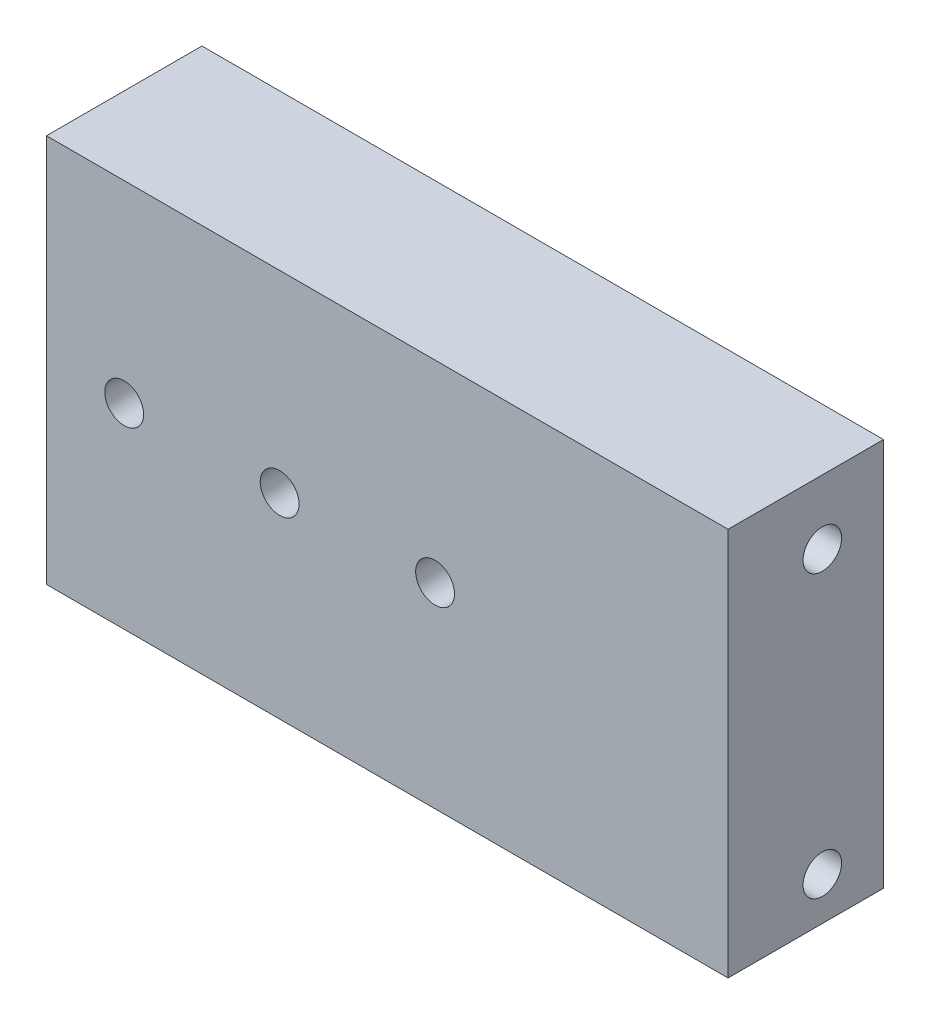
SolidWorks part; units mm, degrees
material "Delrin 2700 NC010, Low Viscosity Acetal Copolymer (SS)"
ref_plane "Front Plane" through (0, 0, 0) normal (0, 0, 1) x (1, 0, 0)
ref_plane "Top Plane" through (0, 0, 0) normal (0, 1, 0) x (1, 0, 0)
ref_plane "Right Plane" through (0, 0, 0) normal (1, 0, 0) x (0, 0, -1)
sketch "Sketch1" plane through (0, 0, 0) normal (1, 0, 0) x (0, 0, -1)
  line L0 (25.4, 0) -> (25.4, 108.2)
  line L1 (0, 0) -> (25.4, 0)
  line L2 (0, 0) -> (0, 63.5)
  line L3 (0, 63.5) -> (25.4, 63.5)
  line L4 (25.4, 0) -> (25.4, 63.5)
  line L5 (25.4, 108.2) -> (0, 108.2)
  line L6 (0, 108.2) -> (0, 0)
  line L7 (25.4, 108.2) -> (228.6, 108.2) construction
  dimension "D1" = 25.4
  dimension "D2" = 63.5
  dimension "D3" = 44.7
extrude "Boss-Extrude1" add sketch "Sketch1" against normal up to surface (111.376 mm away) contours L2 L1 L0 L3
hole_wizard "1/4 (0.25) Diameter Hole1" positions "Sketch2" profile "Sketch3" hole size "1/4" standard "ANSI Inch" end condition through all
sketch "Sketch2" plane through (0, 0, 0) normal (0, 0, 1) x (1, 0, 0)
  point P0 (-98.676, 32)
  point P3 (-47.876, 32)
  point P6 (-73.276, 32)
sketch "Sketch3" plane through (-98.676, 32, 0) normal (1, 0, 0) x (0, -1, 0)
  line L0 (0, 0) -> (0, 25.4)
  line L1 (0, 25.4) -> (3.175, 25.4)
  line L2 (3.175, 25.4) -> (3.175, 0)
  line L5 (3.175, 0) -> (0, 0)
  line L11 (0, -6.35) -> (0, 107.95) construction
  dimension "Thru Hole Dia." = 6.35
  dimension "Thru Hole Depth" = 25.4
hole_wizard "Ø6.0mm Dowel Hole1" positions "Sketch4" profile "Sketch6" hole size "Ø6.0" standard "ANSI Metric"
sketch "Sketch4" plane through (0, 0, 0) normal (1, 0, 0) x (0, 0, -1)
  point P0 (15.4, 7)
  point P3 (15.4, 53)
sketch "Sketch6" plane through (0, 7, -15.4) normal (0, 1, 0) x (0, 0, -1)
  line L0 (0, 0) -> (0, 10.8927)
  line L1 (0, 10.8927) -> (3.15, 9)
  line L2 (3.15, 9) -> (3.15, 0)
  line L5 (3.15, 0) -> (0, 0)
  line L10 (0, 10.8927) -> (-3.15, 9) construction
  line L11 (0, -6.35) -> (0, 107.95) construction
  dimension "Hole Dia." = 6.3
  dimension "Hole Depth" = 9
  dimension "Drill Angle" = 118
